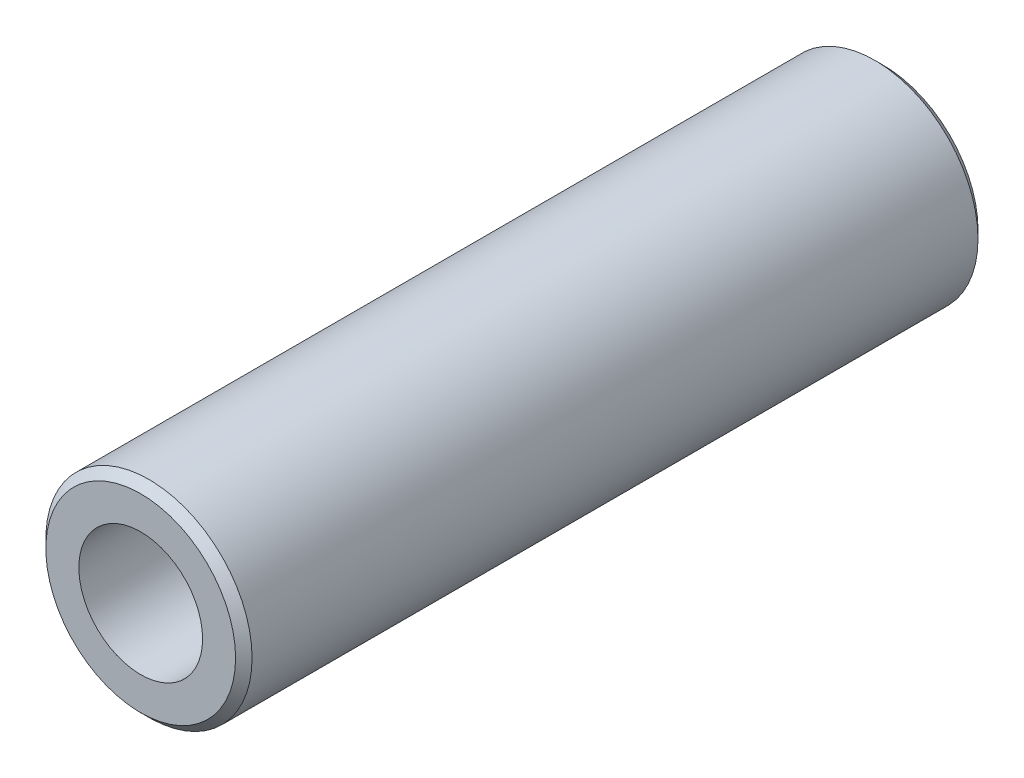
SolidWorks part; units mm, degrees
ref_plane "Front Plane" through (0, 0, 0) normal (0, 0, 1) x (1, 0, 0)
ref_plane "Top Plane" through (0, 0, 0) normal (0, 1, 0) x (1, 0, 0)
ref_plane "Right Plane" through (0, 0, 0) normal (1, 0, 0) x (0, 0, -1)
sketch "Sketch1" plane through (0, 0, 0) normal (0, 0, 1) x (1, 0, 0)
  circle A0 centre (0, 0) radius 6.25
  dimension "D1" = 12.5
extrude "Extrude-Thin1" add sketch "Sketch1" along normal mid plane 45 thin thin type one direction reverse wall 2.5
chamfer "Chamfer1" distance 0.5 angle 45 2 edges at (6.25, 0, -22.5) (6.25, 0, 22.5)
